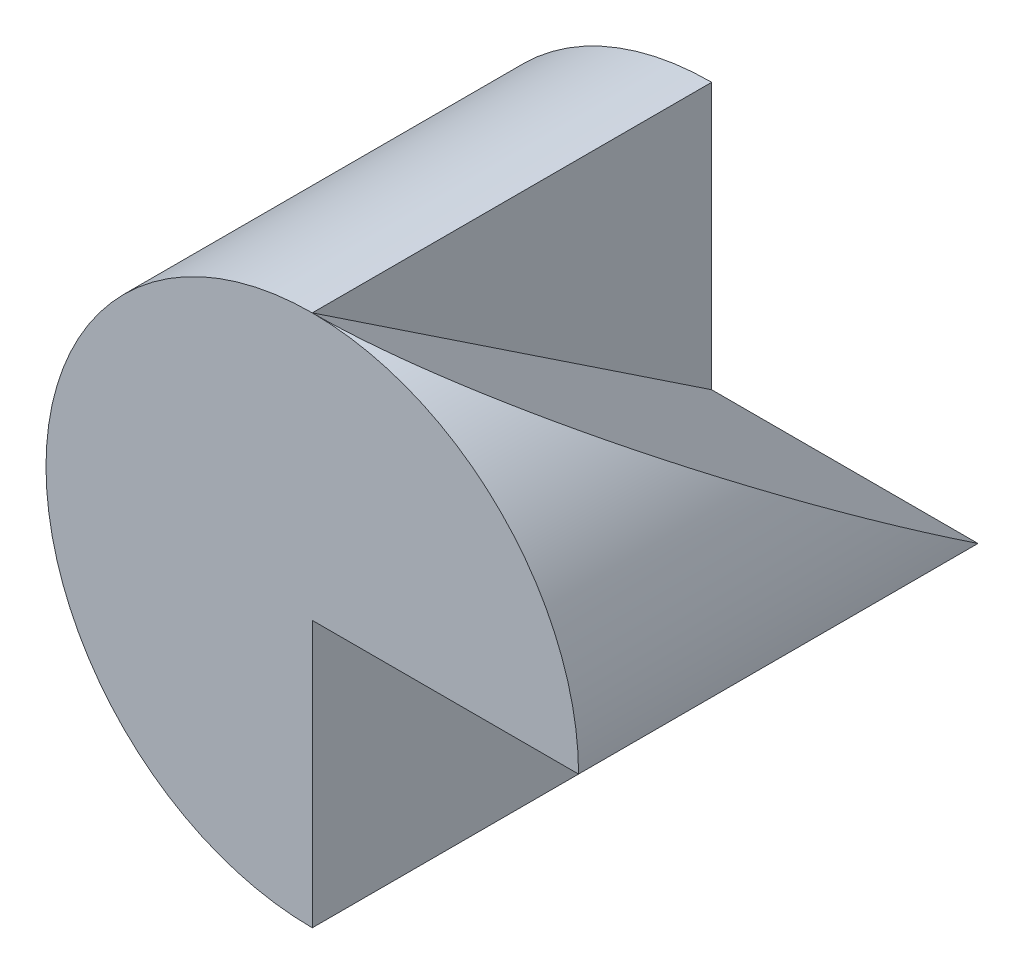
SolidWorks part; units mm, degrees
ref_plane "Front Plane" through (0, 0, 0) normal (0, 0, 1) x (1, 0, 0)
ref_plane "Top Plane" through (0, 0, 0) normal (0, 1, 0) x (1, 0, 0)
ref_plane "Right Plane" through (0, 0, 0) normal (1, 0, 0) x (0, 0, -1)
sketch "Sketch1" plane through (0, 0, 0) normal (0, 0, 1) x (1, 0, 0)
  circle A0 centre (0, 0) radius 10
  dimension "D1" = 20
extrude "Boss-Extrude1" add sketch "Sketch1" along normal blind 15
sketch "Sketch2" plane through (0, 0, 15) normal (0, 0, 1) x (1, 0, 0)
  line L0 (0, 0) -> (10, 0)
  line L1 (0, 0) -> (0, -10)
  circle A0 centre (0, 0) radius 10 construction
  arc A1 (0, -10) -> (10, 0) centre (0, 0) ccw
  circle M1 centre (0, 0) radius 10
extrude "Cut-Extrude1" cut sketch "Sketch2" against normal through all contours L0 L1 M1
ref_plane "Plane1" through (0, 10, 0) normal (0, 1, 0) x (1, 0, 0)
sketch "Sketch3" plane through (0, 10, 0) normal (0, 1, 0) x (1, 0, 0)
  point P0 (0, -14.8602)
ref_plane "Plane2" through (10, 0, 0) normal (1, 0, 0) x (0, 0, -1)
sketch "Sketch5" plane through (10, 0, 0) normal (1, 0, 0) x (0, 0, -1)
  line L0 (0, 0) -> (0, 10)
  line L1 (0, 10) -> (-15, 10)
  line L2 (-15, 10) -> (0, 0)
  dimension "D1" = 10
  dimension "D2" = 15
extrude "Cut-Extrude2" cut sketch "Sketch5" against normal blind 10
